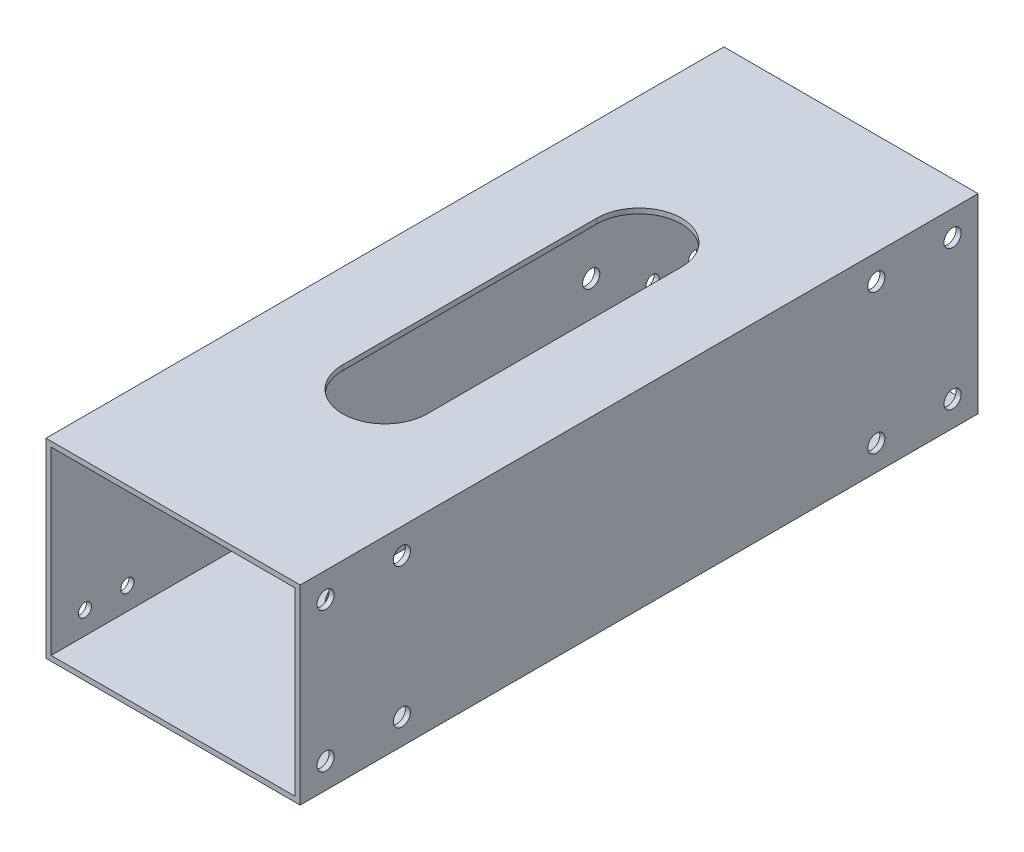
SolidWorks part; units mm, degrees
material "6063-T5"
ref_plane "前视基准面" through (0, 0, 0) normal (0, 0, 1) x (1, 0, 0)
ref_plane "上视基准面" through (0, 0, 0) normal (0, 1, 0) x (1, 0, 0)
ref_plane "右视基准面" through (0, 0, 0) normal (1, 0, 0) x (0, 0, -1)
sketch "草图1" plane through (0, 0, 0) normal (0, 0, 1) x (1, 0, 0)
  line L0 (-28.8, -21.3) -> (-28.8, 21.3)
  line L1 (-30, -22.5) -> (30, -22.5)
  line L2 (-30, -22.5) -> (-30, 22.5)
  line L3 (-30, 22.5) -> (30, 22.5)
  line L4 (30, -22.5) -> (30, 22.5)
  line L5 (0, 22.5) -> (0, -22.5) construction
  line L6 (-30, 0) -> (30, 0) construction
  line L7 (-28.8, 21.3) -> (28.8, 21.3)
  line L8 (28.8, -21.3) -> (28.8, 21.3)
  line L9 (-28.8, -21.3) -> (28.8, -21.3)
  point P0 (0, 0)
  dimension "D1" = 60
  dimension "D2" = 45
  dimension "D3" = 1.2
extrude "凸台-拉伸1" add sketch "草图1" along normal mid plane 160
sketch "草图4" plane through (30, 0, 0) normal (1, 0, 0) x (0, 0, -1)
  line L0 (-65, 0) -> (65, 0) construction
  line L1 (-80, -22.5) -> (-80, 22.5) construction
  line L2 (-80, -22.5) -> (-50, -22.5) construction
  line L3 (-80, -22.5) -> (-80, 22.5) construction
  line L4 (-80, 22.5) -> (-50, 22.5) construction
  line L5 (-50, -22.5) -> (-50, 22.5) construction
  line L6 (-65, 22.5) -> (-65, -22.5) construction
  line L7 (-80, 0) -> (-50, 0) construction
  line L8 (-80, 22.5) -> (80, 22.5) construction
  line L10 (-74, -16.5) -> (-56, -16.5) construction
  line L11 (-74, -16.5) -> (-74, 16.5) construction
  line L12 (-74, 16.5) -> (-56, 16.5) construction
  line L13 (-56, -16.5) -> (-56, 16.5) construction
  line L14 (-65, 16.5) -> (-65, -16.5) construction
  line L15 (-74, 0) -> (-56, 0) construction
  circle A0 centre (-74, 16.5) radius 2.025
  circle A1 centre (-56, 16.5) radius 2.025
  circle A2 centre (-74, -16.5) radius 2.025
  circle A3 centre (-56, -16.5) radius 2.025
  point P4 (0, 0)
  dimension "D4" = 4.05
  dimension "D1" = 30
  dimension "D2" = 6
  dimension "D3" = 6
extrude "切除-拉伸1" cut sketch "草图4" against normal mid plane 10
mirror "镜向1" about plane through (0, 0, 0) normal (0, 0, 1) of "切除-拉伸1"
sketch "草图5" plane through (-30, 0, 0) normal (-1, 0, 0) x (0, 0, 1)
  circle A0 centre (62, 16) radius 1.55 construction
  circle A1 centre (72, 16) radius 1.55 construction
  circle A2 centre (62, -16) radius 1.55 construction
  circle A3 centre (72, -16) radius 1.55 construction
  circle A4 centre (62, 16) radius 1.55
  circle A5 centre (72, 16) radius 1.55
  circle A6 centre (62, -16) radius 1.55
  circle A7 centre (72, -16) radius 1.55
extrude "切除-拉伸2" cut sketch "草图5" against normal mid plane 10
mirror "镜向2" about plane through (0, 0, 0) normal (0, 0, 1) of "切除-拉伸2"
sketch "草图6" plane through (-30, 0, 0) normal (-1, 0, 0) x (0, 0, 1)
  line L0 (80, 22.5) -> (-80, 22.5) construction
  line L1 (0, 0) -> (0, 22.5) construction
  circle A0 centre (47.5, 17) radius 1.65 construction
  circle A1 centre (47.5, -8) radius 1.65 construction
  circle A2 centre (47.5, 17) radius 1.65 construction
  circle A3 centre (47.5, -8) radius 1.65 construction
  circle A4 centre (47.5, -8) radius 2.025
  circle A5 centre (47.5, 17) radius 2.025
  circle A6 centre (-47.5, -8) radius 1.65 construction
  circle A7 centre (-47.5, 17) radius 1.65 construction
  circle A8 centre (-47.5, 17) radius 2.025
  circle A9 centre (-47.5, -8) radius 2.025
  dimension "D1" = 4.05
extrude "切除-拉伸3" cut sketch "草图6" against normal up to surface (1.2 mm away) up to face at (-28.8, 16, -73.55)
sketch "草图7" plane through (0, -22.5, 0) normal (0, -1, 0) x (1, 0, 0)
  line L0 (0, -30) -> (0, 30) construction
  line L1 (-10, -30) -> (-10, 30)
  line L2 (10, -30) -> (10, 30)
  arc A0 (-10, -30) -> (10, -30) centre (0, -30) ccw
  arc A1 (10, 30) -> (-10, 30) centre (0, 30) ccw
  point P2 (0, 0)
  dimension "D2" = 10
  dimension "D1" = 60
extrude "切除-拉伸4" cut sketch "草图7" against normal blind 160
